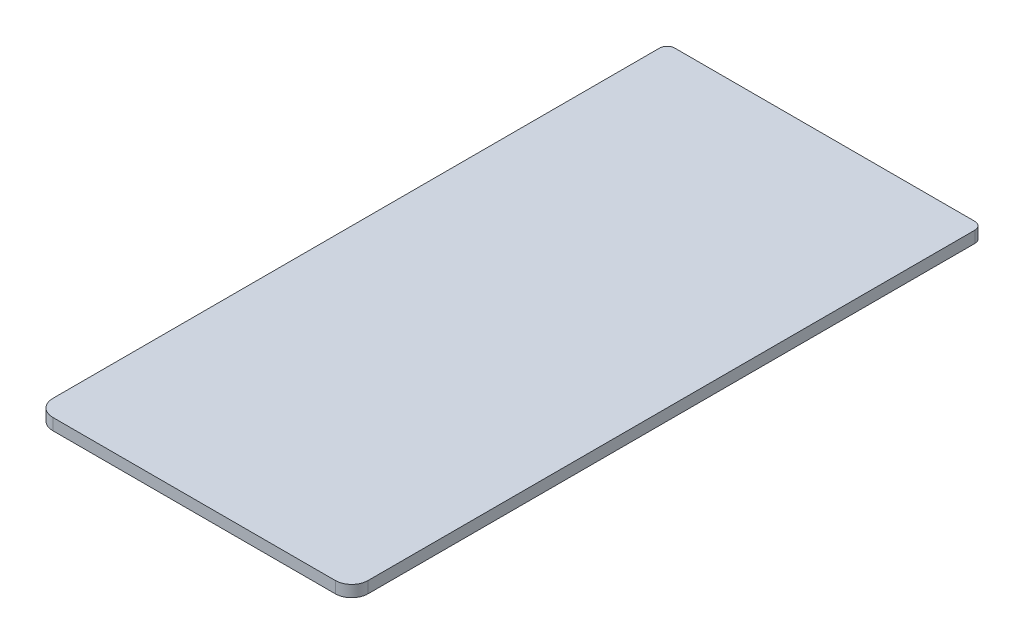
SolidWorks part; units mm, degrees
material "Verre"
ref_plane "Plan de face" through (0, 0, 0) normal (0, 0, 1) x (1, 0, 0)
ref_plane "Plan de dessus" through (0, 0, 0) normal (0, 1, 0) x (1, 0, 0)
ref_plane "Plan de droite" through (0, 0, 0) normal (1, 0, 0) x (0, 0, -1)
sketch "Esquisse1" plane through (0, 0, 0) normal (0, 1, 0) x (1, 0, 0)
  line L0 (-12.99, 27.312) -> (12.99, 27.312)
  line L1 (-13.6525, 26.6495) -> (-13.6525, -25.892)
  line L2 (-12.2325, -27.312) -> (12.2325, -27.312)
  line L3 (13.6525, 26.6495) -> (13.6525, -25.892)
  arc A0 (-13.6525, -25.892) -> (-12.2325, -27.312) centre (-12.2325, -25.892) ccw
  arc A1 (12.2325, -27.312) -> (13.6525, -25.892) centre (12.2325, -25.892) ccw
  arc A2 (12.99, 27.312) -> (13.6525, 26.6495) centre (12.99, 26.6495) cw
  arc A3 (-12.99, 27.312) -> (-13.6525, 26.6495) centre (-12.99, 26.6495) ccw
extrude "Boss.-Extru.1" add sketch "Esquisse1" along normal blind 1
